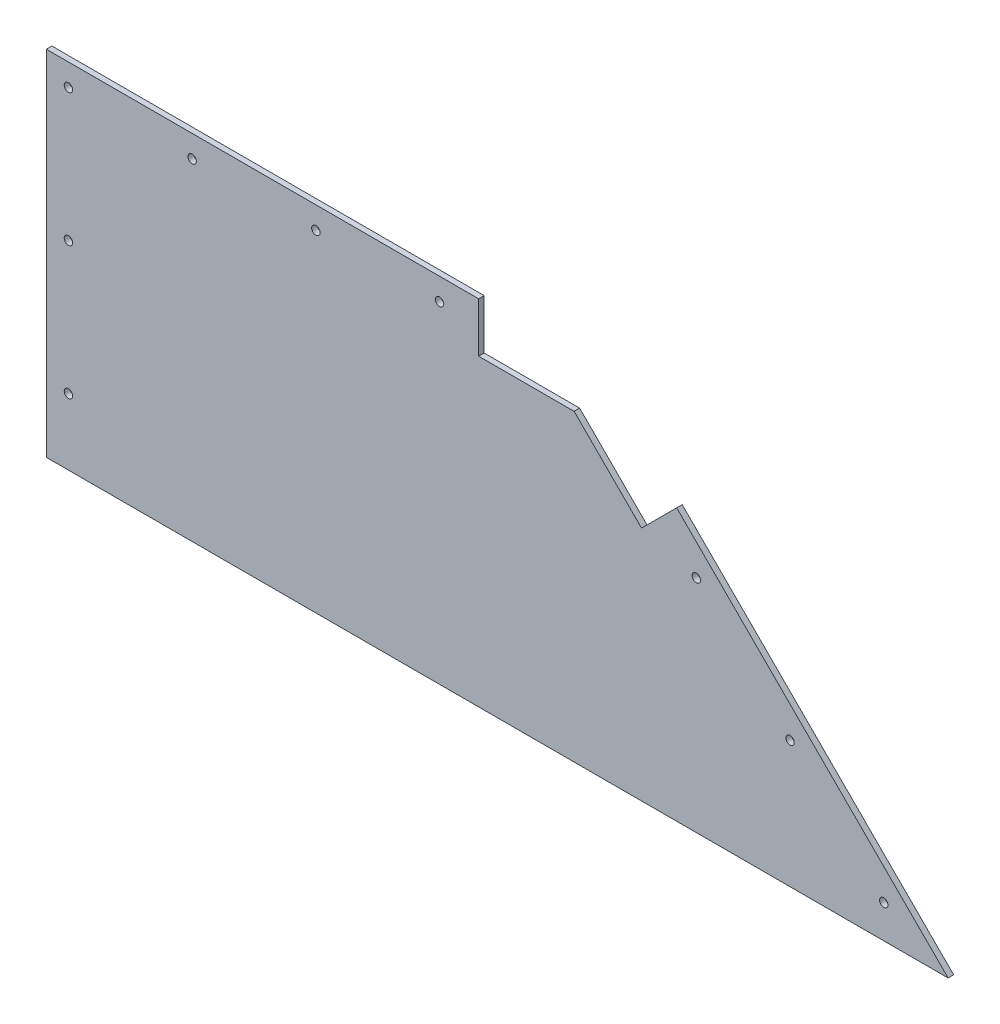
SolidWorks part; units mm, degrees
ref_plane "Front Plane" through (0, 0, 0) normal (0, 0, 1) x (1, 0, 0)
ref_plane "Top Plane" through (0, 0, 0) normal (0, 1, 0) x (1, 0, 0)
ref_plane "Right Plane" through (0, 0, 0) normal (1, 0, 0) x (0, 0, -1)
sketch "Sketch1" plane through (0, 0, 0) normal (0, 0, 1) x (1, 0, 0)
  line L0 (315.214, 203.2) -> (518.414, 0)
  line L1 (0, 0) -> (127, 0)
  line L2 (0, 0) -> (0, 203.2)
  line L3 (0, 203.2) -> (315.214, 203.2)
  line L5 (518.414, 0) -> (127, 0)
  dimension "D1" = 315.214
  dimension "D2" = 203.2
  dimension "D3" = 45
extrude "Boss-Extrude1" add sketch "Sketch1" along normal blind 3.175
sketch "Sketch2" plane through (0, 0, 3.175) normal (0, 0, 1) x (1, 0, 0)
  line L0 (12.7, 203.2) -> (12.7, 0) construction
  line L4 (315.214, 203.2) -> (0, 203.2) construction
  line L7 (0, 0) -> (518.414, 0) construction
  line L8 (12.7, 190.5) -> (327.914, 190.5) construction
  line L9 (518.414, 0) -> (315.214, 203.2) construction
  line L10 (0, 203.2) -> (0, 0) construction
  circle A7 centre (12.7, 190.5) radius 2.413
  circle A8 centre (83.82, 190.5) radius 2.413
  circle A9 centre (154.94, 190.5) radius 2.413
  circle A10 centre (226.06, 190.5) radius 2.413
  circle A11 centre (12.7, 114.3) radius 2.413
  circle A12 centre (12.7, 38.1) radius 2.413
  dimension "D2" = 12.7
  dimension "D3" = 4.826
  dimension "D4" = 4
  dimension "D1" = 12.7
  dimension "D5" = 3
extrude "Cut-Extrude1" cut sketch "Sketch2" against normal up to next
sketch "Sketch3" plane through (0, 0, 3.175) normal (0, 0, 1) x (1, 0, 0)
  line L0 (500.4535, 0) -> (297.2535, 203.2) construction
  line L1 (0, 0) -> (518.414, 0) construction
  line L2 (315.214, 203.2) -> (0, 203.2) construction
  line L4 (315.214, 203.2) -> (518.414, 0) construction
  circle A0 centre (481.4035, 19.05) radius 2.413
  circle A1 centre (427.522, 72.9315) radius 2.413
  circle A2 centre (373.6404, 126.8131) radius 2.413
  circle A3 centre (319.7589, 180.6946) radius 2.413
  dimension "D2" = 4.826
  dimension "D3" = 19.05
  dimension "D1" = 12.7
  dimension "D4" = 4
extrude "Cut-Extrude2" cut sketch "Sketch3" against normal up to next
sketch "Sketch4" plane through (0, 0, 3.175) normal (0, 0, 1) x (1, 0, 0)
  line L0 (315.214, 203.2) -> (248.539, 203.2)
  line L1 (315.214, 203.2) -> (0, 203.2) construction
  line L2 (248.539, 203.2) -> (248.539, 174.625)
  line L3 (248.539, 174.625) -> (303.3778, 174.625)
  line L4 (303.3778, 174.625) -> (342.1548, 135.8481)
  line L5 (342.1548, 135.8481) -> (362.3603, 156.0537)
  line L6 (518.414, 0) -> (315.214, 203.2) construction
  line L7 (362.3603, 156.0537) -> (315.214, 203.2)
  dimension "D1" = 66.675
  dimension "D2" = 66.675
  dimension "D3" = 28.575
  dimension "D4" = 28.575
  dimension "D5" = 135
extrude "Cut-Extrude3" cut sketch "Sketch4" against normal up to next
